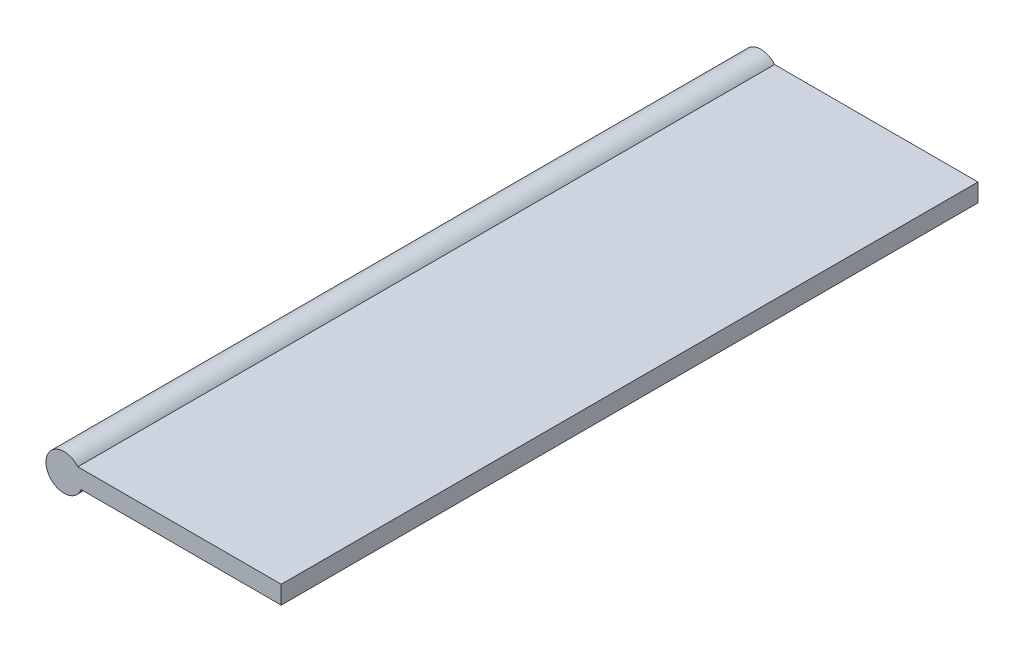
SolidWorks part; units mm, degrees
ref_plane "Front Plane" through (0, 0, 0) normal (0, 0, 1) x (1, 0, 0)
ref_plane "Top Plane" through (0, 0, 0) normal (0, 1, 0) x (1, 0, 0)
ref_plane "Right Plane" through (0, 0, 0) normal (1, 0, 0) x (0, 0, -1)
sketch "Sketch1" plane through (0, 0, 0) normal (0, 0, 1) x (1, 0, 0)
  circle A0 centre (0, 0) radius 2.54
  dimension "D1" = 5.08
extrude "Boss-Extrude1" add sketch "Sketch1" along normal blind 97.79
sketch "Sketch2" plane through (0, 0, 0) normal (1, 0, 0) x (0, 0, -1)
  line L0 (-97.79, 2.54) -> (-97.79, -2.54) construction
  line L1 (-97.79, 1.6502) -> (0, 1.6502)
  line L2 (-97.79, 1.6502) -> (-97.79, -0.8898)
  line L3 (-97.79, -0.8898) -> (0, -0.8898)
  line L4 (0, 1.6502) -> (0, -0.8898)
  line L5 (0, 2.794) -> (0, -2.794) construction
  line L6 (2.794, 0) -> (-2.794, 0) construction
  dimension "D1" = 2.54
  dimension "D2" = 1.6502
extrude "Boss-Extrude2" add sketch "Sketch2" along normal blind 30.48
